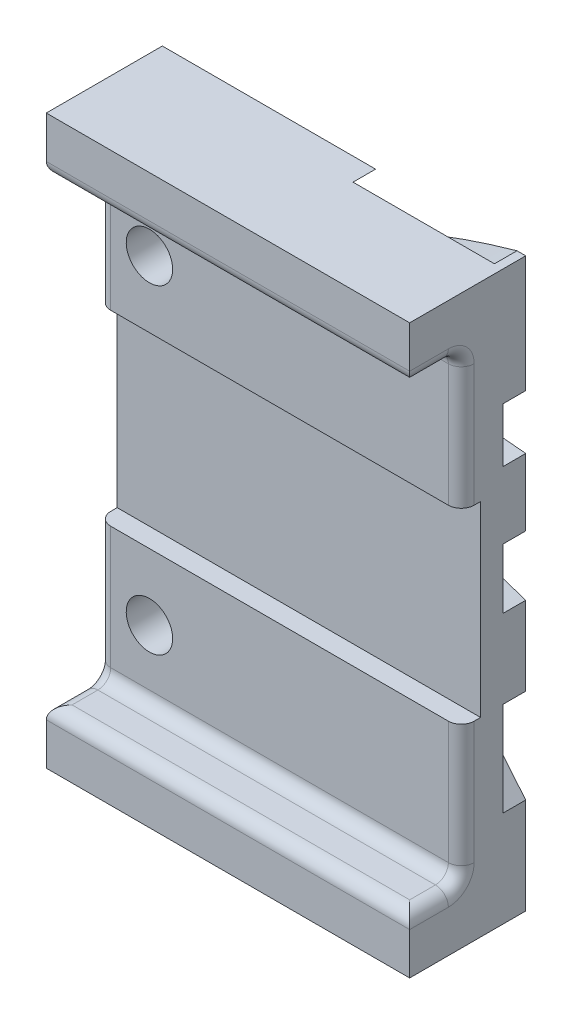
SolidWorks part; units mm, degrees
ref_plane "Front Plane" through (0, 0, 0) normal (0, 0, 1) x (1, 0, 0)
ref_plane "Top Plane" through (0, 0, 0) normal (0, 1, 0) x (1, 0, 0)
ref_plane "Right Plane" through (0, 0, 0) normal (1, 0, 0) x (0, 0, -1)
sketch "Sketch1" plane through (0, 0, 0) normal (0, 0, 1) x (1, 0, 0)
  line L1 (-14.09, -22) -> (14.09, -22)
  line L2 (-14.09, -22) -> (-14.09, 22)
  line L3 (-14.09, 22) -> (14.09, 22)
  line L4 (14.09, -22) -> (14.09, 22)
  line L5 (-14.09, -22) -> (14.09, 22) construction
  line L6 (-14.09, 22) -> (14.09, -22) construction
  point P0 (0, 0)
  dimension "D1" = 44
  dimension "D2" = 28.18
extrude "Boss-Extrude1" add sketch "Sketch1" along normal blind 11 and the other way blind 2
sketch "Sketch3" plane through (-14.09, 0, 0) normal (-1, 0, 0) x (0, 0, 1)
  line L0 (8, 7.25) -> (11, 7.25)
  line L5 (8, 17.75) -> (3, 17.75)
  line L6 (8, 17.75) -> (8, 7.25)
  line L7 (8, -17.75) -> (3, -17.75)
  line L8 (3, 17.75) -> (3, 7.25)
  line L9 (11, -7.25) -> (8, -7.25)
  line L10 (8, -7.25) -> (8, -17.75)
  line L13 (3, -7.25) -> (1.5034, -7.25)
  line L14 (11, 7.25) -> (11, -7.25)
  line L15 (14.8907, 0) -> (-5.9971, 0) construction
  line L16 (3, 7.25) -> (1.5034, 7.25)
  line L17 (1.5034, 7.25) -> (1.5034, -7.25)
  line L18 (3, -7.25) -> (3, -17.75)
  dimension "D1" = 3
  dimension "D2" = 5
  dimension "D3" = 35.5
extrude "Cut-Extrude1" cut sketch "Sketch3" against normal blind 37
sketch "Sketch4" plane through (0, -22, 0) normal (0, -1, 0) x (1, 0, 0)
  line L0 (-14.09, 11) -> (14.09, 11) construction
  line L1 (-6.09, 11) -> (14.09, 11)
  line L2 (-6.09, 11) -> (-6.09, 7)
  line L3 (-6.09, 7) -> (14.09, 7)
  line L4 (14.09, 11) -> (14.09, 7)
  line L5 (14.09, -2) -> (14.09, 11) construction
  line L6 (-14.09, -2) -> (-14.09, 11) construction
  dimension "D1" = 4
  dimension "D2" = 8
extrude "Cut-Extrude2" cut sketch "Sketch4" against normal blind 48
sketch "Sketch5" plane through (0, 0, -2) normal (0, 0, -1) x (-1, 0, 0)
  line L0 (14.09, 4.4317) -> (14.09, 4.2995)
  line L1 (-14.09, 22) -> (14.09, 22) construction
  line L2 (-2.4482, 22) -> (-13.4131, 22)
  line L3 (14.09, 4.4317) -> (14.09, 4.2995)
  line L4 (5.5922, -22) -> (0.0012, -22)
  line L5 (-14.09, 12.9435) -> (-14.09, 8.7272)
  line L6 (-2.4482, 22) -> (-13.4131, 22)
  line L7 (5.5922, -22) -> (0.0012, -22)
  line L8 (-5.5133, -22) -> (-9.4224, -22)
  line L9 (-14.09, 12.9435) -> (-14.09, 8.7272)
  line L10 (-14.09, 3.5233) -> (-14.09, -1.1313)
  line L11 (-14.09, -7.2405) -> (-14.09, -14.5457)
  line L12 (-5.5133, -22) -> (-9.4224, -22)
  line L13 (14.09, 22) -> (14.09, -22) construction
  line L14 (14.09, -22) -> (-14.09, -22) construction
  line L15 (-14.09, -22) -> (-14.09, 22) construction
  spline S0 degree 3 poles (-2.4482, 22) (19.5671, 11.5364) (5.1516, -7.6222) (5.5922, -22) knots 0 0 0 0 0.832841 0.832841 0.832841 0.832841
  spline S1 degree 3 poles (-13.4131, 22) (18.4961, 13.0475) (3.5462, -4.8632) (0.0012, -22) knots 0 0 0 0 0.886772 0.886772 0.886772 0.886772
  spline S2 degree 3 poles (-14.09, 12.9435) (17.0272, 14.2309) (-0.9132, -5.6377) (-5.5133, -22) knots 0 0 0 0 0.882154 0.882154 0.882154 0.882154
  spline S3 degree 3 poles (-14.09, 8.7272) (12.7104, 11.6786) (-5.2505, -7.0269) (-9.4224, -22) knots 0 0 0 0 0.871233 0.871233 0.871233 0.871233
  spline S4 degree 2 poles (-14.09, 3.5233) (7.9134, 11.6377) (-14.09, -14.5457) knots 0 0 0 1 1 1
  spline S5 degree 2 poles (-14.09, -1.1313) (-1.6541, 3.2119) (-14.09, -7.2405) knots 0 0 0 1 1 1
  line M1 (-14.09, 22) -> (-14.09, -22)
  line M2 (-14.09, -22) -> (14.09, -22)
  line M4 (14.09, 22) -> (-14.09, 22)
extrude "Cut-Extrude3" cut sketch "Sketch5" against normal blind 1.75 contours S3 S2 M1 M2 | S5 S4 M1 | S1 S0 M4 M2
sketch "Sketch7" plane through (0, 0, 11) normal (0, 0, 1) x (1, 0, 0)
  line L3 (-31.6118, 0) -> (31.371, 0) construction
  line L4 (-10.09, 22.9416) -> (-10.09, 7.5663) construction
  line L5 (-6.09, 22) -> (-6.09, 7.25) construction
  line L6 (-14.09, 22) -> (-14.09, 7.25) construction
  circle A0 centre (-10.09, 12.4) radius 1.8
  circle A1 centre (-10.09, -12.4) radius 1.8
  dimension "D1" = 3.6
  dimension "D2" = 24.8
extrude "Cut-Extrude4" cut sketch "Sketch7" against normal blind 23
sketch "Sketch10" plane through (0, 22, 0) normal (0, 1, 0) x (1, 0, 0)
  line L1 (-4.8142, -11.586) -> (-16.61, -11.586)
  line L2 (-4.8142, -11.586) -> (-4.8142, -7)
  line L3 (-4.8142, -7) -> (-16.61, -7)
  line L4 (-16.61, -11.586) -> (-16.61, -7)
  line L5 (14.09, -7) -> (-6.09, -7) construction
extrude "Cut-Extrude7" cut sketch "Sketch10" against normal blind 53
fillet "Fillet1" radius 1 12 edges at (-14.09, -12.5, 3) (14.09, -12.5, 3) (14.09, 12.5, 3) (-14.09, 12.5, 3) (-14.09, -17.75, 5) (0, -17.75, 3) (14.09, -17.75, 5) (0, -17.75, 7) (14.09, 17.75, 5) (0, 17.75, 3) (-14.09, 17.75, 5) (0, 17.75, 7)
sketch "Sketch8" plane through (0, 0, -2) normal (0, 0, -1) x (-1, 0, 0)
  circle A0 centre (10.09, -12.4) radius 3.25
  circle A1 centre (10.09, 12.4) radius 3.25
  dimension "D1" = 6.5
extrude "Cut-Extrude5" cut sketch "Sketch8" against normal blind 1.75
